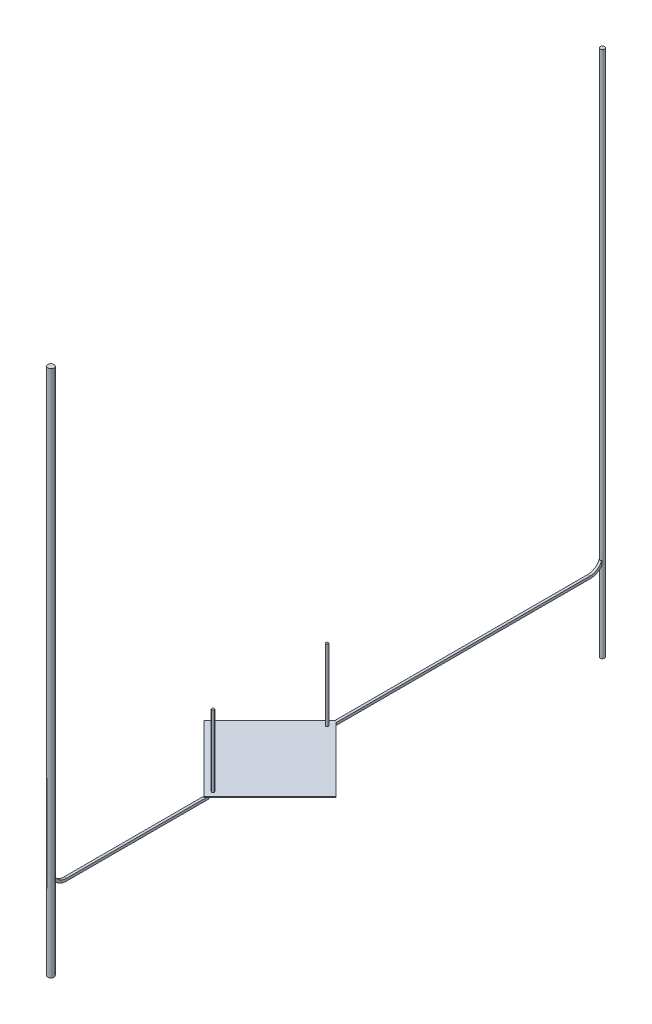
SolidWorks part; units mm, degrees
material "电源线路板"
ref_plane "前视基准面" through (0, 0, 0) normal (0, 0, 1) x (1, 0, 0)
ref_plane "上视基准面" through (0, 0, 0) normal (0, 1, 0) x (1, 0, 0)
ref_plane "右视基准面" through (0, 0, 0) normal (1, 0, 0) x (0, 0, -1)
sketch "草图1" plane through (0, 0, 0) normal (0, 1, 0) x (1, 0, 0)
  line L0 (0, 0) -> (0, 15)
  line L1 (0, 15) -> (15, 15)
  line L2 (15, 15) -> (15, 0)
  line L3 (15, 0) -> (0, 0)
extrude "凸台-拉伸1" add sketch "草图1" along normal blind 0.1
sketch "草图2" plane through (0, 0.1, 0) normal (0, 1, 0) x (1, 0, 0)
  circle A0 centre (1, 1) radius 0.2
  circle A1 centre (14, 14) radius 0.2
extrude "凸台-拉伸2" add sketch "草图2" along normal blind 11.5 separate body
sketch "草图3" plane through (0, 0, 0) normal (0, -1, 0) x (1, 0, 0)
  line L0 (9.5, -14.5) -> (0.5, -14.5)
  line L1 (0.5, -14.5) -> (0.5, -0.5)
  line L2 (0.5, -0.5) -> (7.5, -0.5)
  line L3 (14.5, -14.5) -> (14.5, -9.5)
  line L4 (14.5, -9.5) -> (7.5, -9.5)
  line L5 (8.7, -0.5) -> (9.5, -0.5)
  line L6 (9.5, -14.5) -> (14.5, -14.5)
  line L7 (7.5, -0.5) -> (7.5, -9.5)
  line L9 (8.7, -0.5) -> (8.7, -3)
  line L10 (14.5, -0.5) -> (14.5, -3)
  line L11 (14.5, -3) -> (13.7, -3)
  line L12 (13.7, -3) -> (13.7, -0.5)
  line L13 (13.7, -0.5) -> (14.5, -0.5)
  line L14 (8.7, -3) -> (9.5, -3)
  line L15 (9.5, -3) -> (9.5, -0.5)
extrude "凸台-拉伸3" add sketch "草图3" along normal blind 0.05 separate body
sketch "草图4" plane through (0, 0, 0) normal (0, -1, 0) x (1, 0, 0)
  line L0 (13.7, -0.5) -> (9.5, -0.5)
  line L1 (9.5, -0.5) -> (9.5, -3)
  line L3 (9.5, -3) -> (13.7, -3)
  line L4 (13.7, -0.5) -> (13.7, -3) construction
  line L5 (13.7, -3) -> (13.7, -0.5)
extrude "凸台-拉伸4" add sketch "草图4" along normal blind 0.05 separate body
sketch "草图5" plane through (0, -0.05, 0) normal (0, -1, 0) x (1, 0, 0)
  circle A0 centre (9.1, -0.9) radius 0.1
extrude "凸台-拉伸5" add sketch "草图5" along normal blind 0.3
sketch "草图6" plane through (0, -0.35, 0) normal (0, -1, 0) x (1, 0, 0)
  line L1 (9.5, -0.5) -> (8.7, -0.5) construction
  line L2 (9.1, -0.5) -> (0.5, -0.5)
  line L3 (0.5, -0.5) -> (0.5, -14.5)
  line L4 (0.5, -14.5) -> (9.5, -14.5)
  line L5 (0.5, -14.5) -> (14.5, -14.5) construction
  line L6 (9.5, -14.5) -> (9.5, -0.5)
  line L7 (9.5, -0.5) -> (9.1, -0.5)
extrude "凸台-拉伸6" add sketch "草图6" along normal blind 0.05 separate body
sketch "草图7" plane through (0, -0.05, 0) normal (0, -1, 0) x (1, 0, 0)
  line L3 (13.5, -13.5) -> (12.5, -13.5)
  line L4 (12.5, -13.5) -> (12.5, -12.5)
  line L5 (12.5, -12.5) -> (13.5, -12.5)
  line L6 (13.5, -12.5) -> (13.5, -13.5)
extrude "凸台-拉伸7" add sketch "草图7" along normal blind 0.3 separate body
move or copy body "实体-移动/复制19" bodies to move or copy 109 106 115 108 114 112 113 107 111 copy no translate (-14, 0, 14)
move or copy body "实体-移动/复制20" bodies to move or copy 229 230 232 228 231 224 225 226 227 copy no rotation origin (0, 0, 0) rotation axis (0, 1, 0) rotation angle 45
sketch "草图27" plane through (0, 0, 0) normal (0, 1, 0) x (1, 0, 0)
  circle A0 centre (0, 44.35) radius 0.35
  point P2 (0, 0)
  point P3 (0, 0)
extrude "凸台-拉伸30" add sketch "草图27" along normal blind 72.5 separate body
sketch "草图28" plane through (0, 0, 0) normal (0, 1, 0) x (1, 0, 0)
  circle A0 centre (0, -44.5) radius 0.5
  point P2 (0, 0)
  point P3 (0, 0)
extrude "凸台-拉伸31" add sketch "草图28" along normal blind 72.5 separate body
sketch "草图29" plane through (0, 0, 0) normal (1, 0, 0) x (0, 0, -1)
  line L1 (0, 0) -> (42.2, 0)
  line L2 (0, 0) -> (0, -0.4)
  line L3 (0, -0.4) -> (42.2, -0.4)
  line L4 (42.2, 0) -> (42.2, -0.4)
  line L5 (0, 0) -> (42.2, -0.4) construction
  line L6 (0, -0.4) -> (42.2, 0) construction
  point P4 (21.1, -0.2)
extrude "凸台-拉伸32" add sketch "草图29" along normal mid plane 0.4
sketch "草图33" plane through (0, 0, 0) normal (1, 0, 0) x (0, 0, -1)
  line L0 (-19.799, 0) -> (-9.1924, 0) construction
  line L1 (-19.1952, 0) -> (-42.1952, 0)
  line L2 (-19.1952, 0) -> (-19.1952, -0.4)
  line L3 (-19.1952, -0.4) -> (-42.1952, -0.4)
  line L4 (-42.1952, 0) -> (-42.1952, -0.4)
  line L5 (-19.1952, 0) -> (-42.1952, -0.4) construction
  line L6 (-19.1952, -0.4) -> (-42.1952, 0) construction
  point P4 (-30.6952, -0.2)
extrude "凸台-拉伸34" add sketch "草图33" along normal mid plane 0.4
sketch "草图40" plane through (0, 0, -42.2) normal (0, 0, -1) x (-1, 0, 0)
  line L1 (-0.2, 0) -> (0.2, 0)
  line L2 (-0.2, 0) -> (-0.2, -0.4)
  line L3 (-0.2, -0.4) -> (0.2, -0.4)
  line L4 (0.2, 0) -> (0.2, -0.4)
  line L5 (-0.2, 0) -> (0.2, -0.4) construction
  line L6 (-0.2, -0.4) -> (0.2, 0) construction
  line L7 (-0.2, 0) -> (-0.4, 0)
  line L8 (-0.2, 0) -> (-0.2, 2)
  line L9 (-0.2, 2) -> (-0.4, 2)
  line L10 (-0.4, 0) -> (-0.4, 2)
  line L11 (-0.2, 0) -> (-0.4, 2) construction
  line L12 (-0.2, 2) -> (-0.4, 0) construction
  point P4 (0, -0.2)
  point P10 (-0.3, 1)
revolve "旋转1" add sketch "草图40" angle 90 about L9
sketch "草图41" plane through (0, 0, 42.1952) normal (0, 0, 1) x (1, 0, 0)
  line L1 (-0.2, 0) -> (0.2, 0)
  line L2 (-0.2, 0) -> (-0.2, -0.4)
  line L3 (-0.2, -0.4) -> (0.2, -0.4)
  line L4 (0.2, 0) -> (0.2, -0.4)
  line L5 (-0.2, 0) -> (0.2, -0.4) construction
  line L6 (-0.2, -0.4) -> (0.2, 0) construction
  line L7 (-0.2, 0) -> (-0.4, 0)
  line L8 (-0.2, 0) -> (-0.2, 2)
  line L9 (-0.2, 2) -> (-0.4, 2)
  line L10 (-0.4, 0) -> (-0.4, 2)
  line L11 (-0.2, 0) -> (-0.4, 2) construction
  line L12 (-0.2, 2) -> (-0.4, 0) construction
  point P4 (0, -0.2)
  point P10 (-0.3, 1)
revolve "旋转2" add sketch "草图41" angle 90 about L9
sketch "草图43" plane through (0, 0, 0) normal (0, -1, 0) x (1, 0, 0)
  circle A0 centre (0, -44.35) radius 0.35
extrude "凸台-拉伸35" add sketch "草图43" along normal blind 12.5
sketch "草图44" plane through (0, 0, 0) normal (0, -1, 0) x (1, 0, 0)
  circle A0 centre (0, 44.5) radius 0.5
extrude "凸台-拉伸36" add sketch "草图44" along normal blind 12.5
